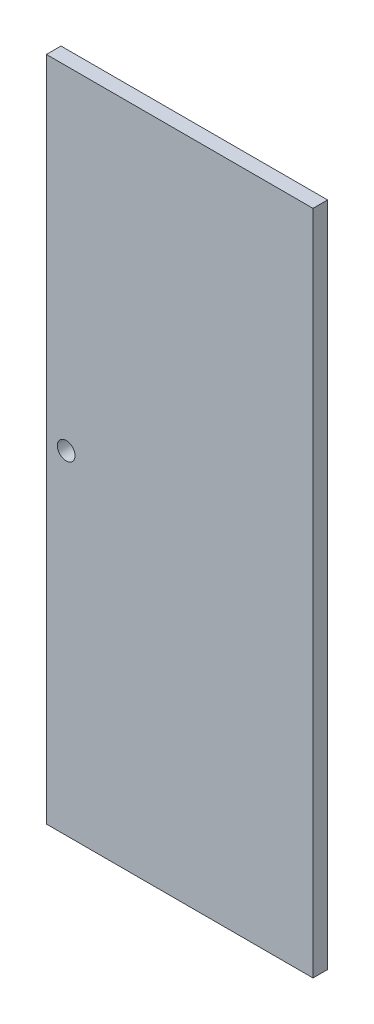
SolidWorks part; units mm, degrees
material "1023 Carbon Steel Sheet (SS)"
ref_plane "Front Plane" through (0, 0, 0) normal (0, 0, 1) x (1, 0, 0)
ref_plane "Top Plane" through (0, 0, 0) normal (0, 1, 0) x (1, 0, 0)
ref_plane "Right Plane" through (0, 0, 0) normal (1, 0, 0) x (0, 0, -1)
sketch "Sketch1" plane through (0, 0, 0) normal (0, 0, 1) x (1, 0, 0)
  line L1 (760.571, 2.3929) -> (1573.371, 2.3929)
  line L2 (760.571, 2.3929) -> (760.571, 2034.3929)
  line L3 (760.571, 2034.3929) -> (1573.371, 2034.3929)
  line L4 (1573.371, 2.3929) -> (1573.371, 2034.3929)
  dimension "D1" = 2032
  dimension "D2" = 812.8
extrude "Boss-Extrude1" add sketch "Sketch1" along normal blind 44.45
sketch "Sketch2" plane through (0, 0, 44.45) normal (0, 0, 1) x (1, 0, 0)
  line L0 (760.571, 2.3929) -> (1573.371, 2.3929) construction
  line L1 (760.571, 2034.3929) -> (760.571, 2.3929) construction
  circle A0 centre (820.896, 1018.3929) radius 26.9875
  dimension "D3" = 53.975
  dimension "D1" = 1016
  dimension "D2" = 60.325
extrude "Cut-Extrude1" cut sketch "Sketch2" against normal blind 44.45
